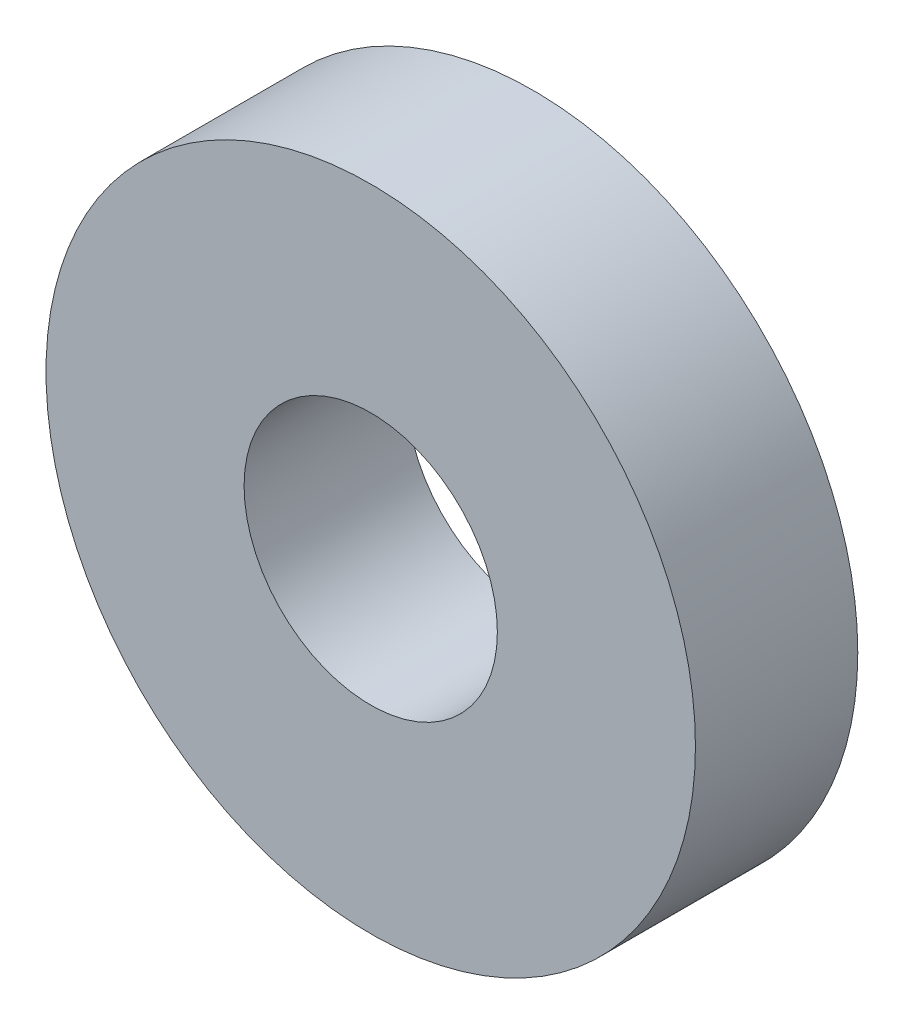
SolidWorks part; units mm, degrees
ref_plane "Front Plane" through (0, 0, 0) normal (0, 0, 1) x (1, 0, 0)
ref_plane "Top Plane" through (0, 0, 0) normal (0, 1, 0) x (1, 0, 0)
ref_plane "Right Plane" through (0, 0, 0) normal (1, 0, 0) x (0, 0, -1)
sketch "Sketch1" plane through (0, 0, 0) normal (0, 0, 1) x (1, 0, 0)
  circle A0 centre (0, 0) radius 10
  circle A1 centre (0, 0) radius 3.9
  dimension "D1" = 20
  dimension "D2" = 7.8
extrude "Boss-Extrude1" add sketch "Sketch1" along normal blind 5
